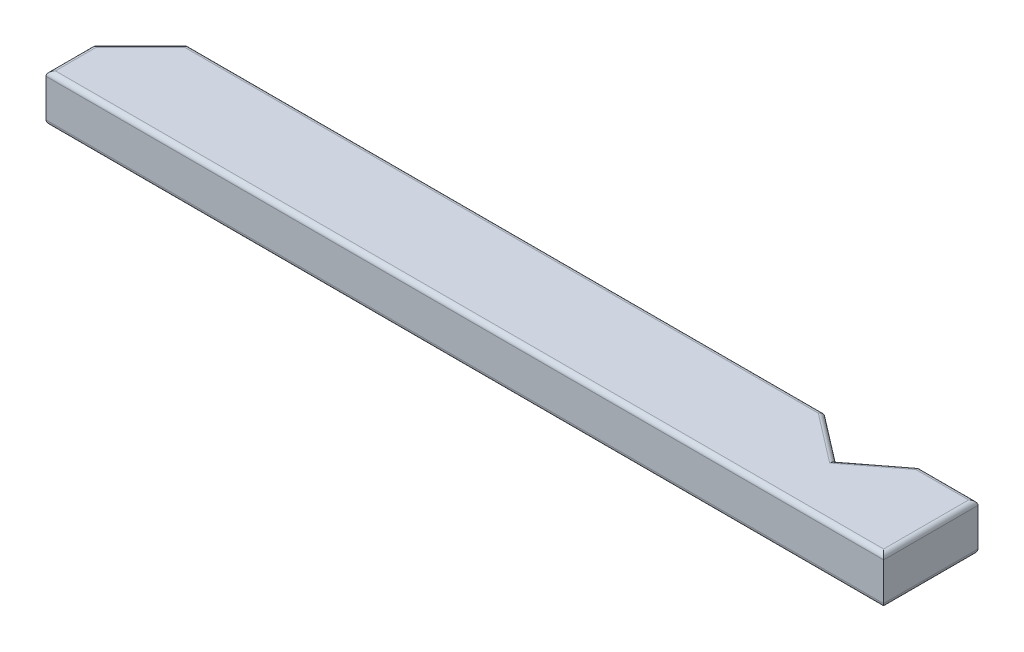
SolidWorks part; units mm, degrees
material "Balsa"
ref_plane "Front Plane" through (0, 0, 0) normal (0, 0, 1) x (1, 0, 0)
ref_plane "Top Plane" through (0, 0, 0) normal (0, 1, 0) x (1, 0, 0)
ref_plane "Right Plane" through (0, 0, 0) normal (1, 0, 0) x (0, 0, -1)
ref_plane "Plane1" through (0, -12.7, 0) normal (0, -1, 0) x (-1, 0, 0)
sketch "Sketch3" plane through (0, -12.7, 0) normal (0, -1, 0) x (-1, 0, 0)
  line L0 (-2600, -287.7) -> (-1803.322, -287.7) construction
  line L1 (-1812.7, -287.7) -> (-2714.3, -287.7)
  line L2 (-1812.7, -287.7) -> (-1812.7, -389.3)
  line L3 (-1812.7, -389.3) -> (-2714.3, -389.3)
  line L4 (-2714.3, -287.7) -> (-2714.3, -389.3)
  line L5 (-2612.7, 275) -> (-2612.7, -275) construction
  line L6 (-1812.7, -275) -> (-1812.7, -347.1543) construction
  dimension "D1" = 101.6
  dimension "D2" = 101.6
extrude "Boss-Extrude3" add sketch "Sketch3" against normal blind 50.8
sketch "Sketch4" plane through (0, 38.1, 0) normal (0, 1, 0) x (1, 0, 0)
  line L0 (2549.2, -287.7) -> (2600, -326.6802)
  line L1 (1812.7, -287.7) -> (2714.3, -287.7) construction
  line L2 (2600, -326.6802) -> (2650.8, -287.7)
  line L3 (2549.2, -287.7) -> (2650.8, -287.7)
  line L4 (2600, -326.6802) -> (2600, -287.7) construction
  line L5 (2714.3, -287.7) -> (2714.3, -389.3) construction
  line L11 (1812.7, -287.7) -> (1812.7, -338.5)
  line L12 (1812.7, -389.3) -> (1812.7, -287.7) construction
  line L13 (1812.7, -338.5) -> (1863.5, -287.7)
  line L14 (1863.5, -287.7) -> (1812.7, -287.7)
  dimension "D1" = 105
  dimension "D2" = 101.6
  dimension "D3" = 114.3
  dimension "D4" = 45
  dimension "D5" = 50.8
extrude "Cut-Extrude1" cut sketch "Sketch4" against normal through all
fillet "Fillet1" radius 5.08 16 edges at (2682.55, 38.1, 287.7) (2682.55, -12.7, 287.7) (2263.5, -12.7, 389.3) (2263.5, 38.1, 389.3) (2714.3, -12.7, 338.5) (2625.4, -12.7, 307.1901) (2574.6, -12.7, 307.1901) (2714.3, 38.1, 338.5) (2625.4, 38.1, 307.1901) (2574.6, 38.1, 307.1901) (1812.7, -12.7, 363.9) (1812.7, 38.1, 363.9) (2206.35, 38.1, 287.7) (2206.35, -12.7, 287.7) (1838.1, -12.7, 313.1) (1838.1, 38.1, 313.1)
